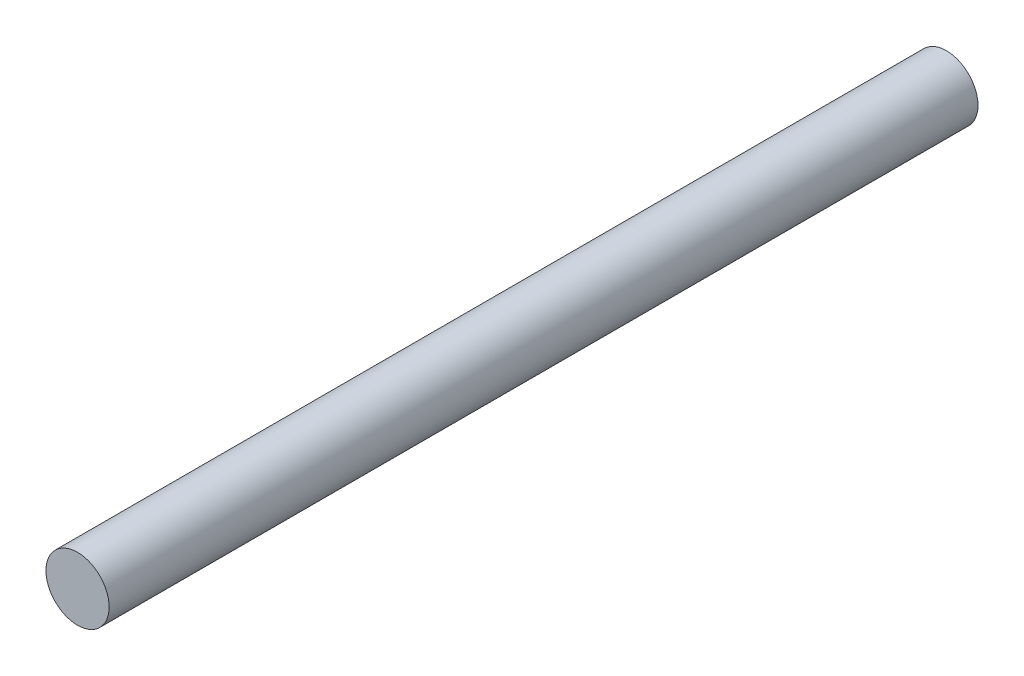
SolidWorks part; units mm, degrees
ref_plane "Front Plane" through (0, 0, 0) normal (0, 0, 1) x (1, 0, 0)
ref_plane "Top Plane" through (0, 0, 0) normal (0, 1, 0) x (1, 0, 0)
ref_plane "Right Plane" through (0, 0, 0) normal (1, 0, 0) x (0, 0, -1)
sketch "Sketch1" plane through (0, 0, 0) normal (0, 0, 1) x (1, 0, 0)
  circle A0 centre (0, 0) radius 4
  dimension "D1" = 8
extrude "Boss-Extrude1" add sketch "Sketch1" along normal blind 110
